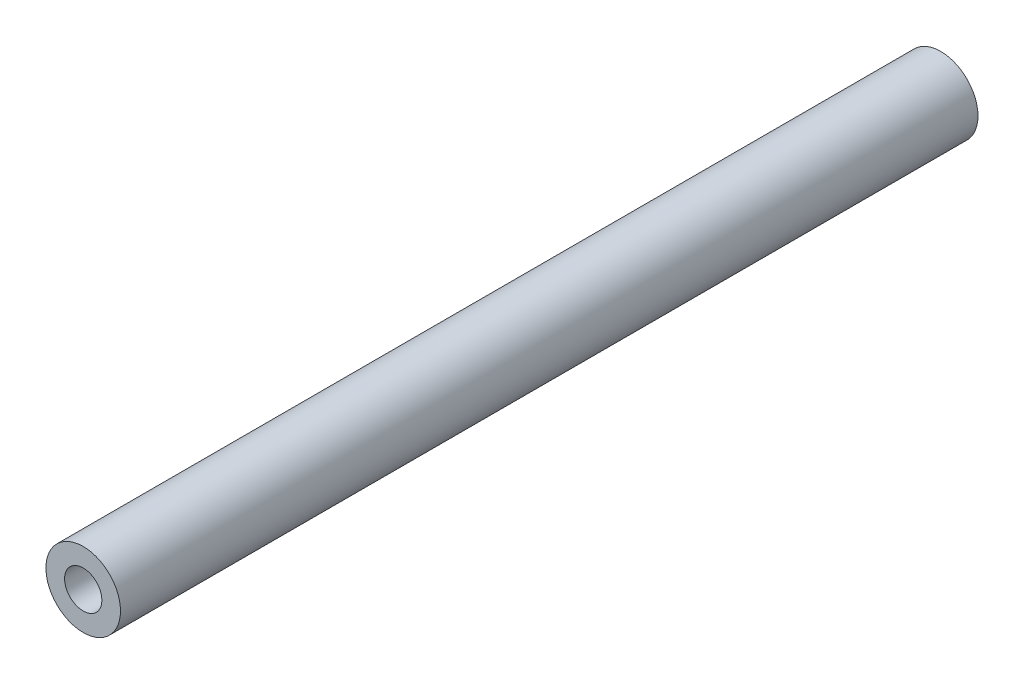
SolidWorks part; units mm, degrees
material "PTFE (general)"
ref_plane "Front Plane" through (0, 0, 0) normal (0, 0, 1) x (1, 0, 0)
ref_plane "Top Plane" through (0, 0, 0) normal (0, 1, 0) x (1, 0, 0)
ref_plane "Right Plane" through (0, 0, 0) normal (1, 0, 0) x (0, 0, -1)
sketch "Sketch1" plane through (0, 0, 0) normal (0, 0, 1) x (1, 0, 0)
  circle A0 centre (0, 0) radius 2
  circle A1 centre (0, 0) radius 1
  dimension "D1" = 4
  dimension "D2" = 2
extrude "Boss-Extrude1" add sketch "Sketch1" along normal blind 46
